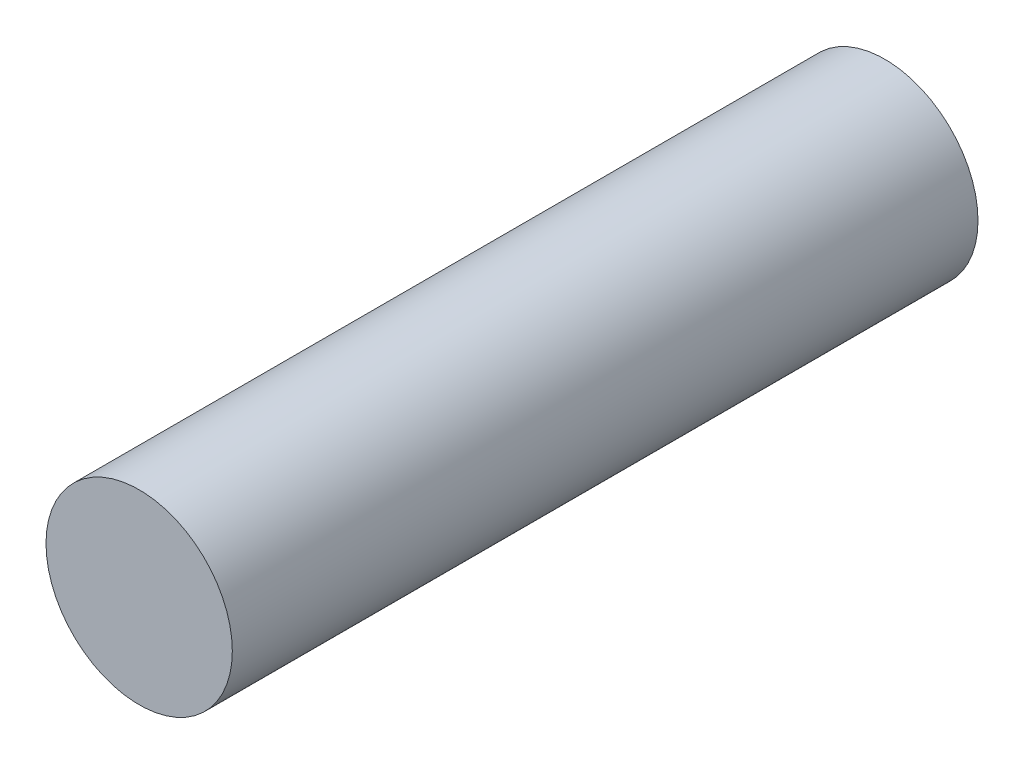
SolidWorks part; units mm, degrees
ref_plane "Front Plane" through (0, 0, 0) normal (0, 0, 1) x (1, 0, 0)
ref_plane "Top Plane" through (0, 0, 0) normal (0, 1, 0) x (1, 0, 0)
ref_plane "Right Plane" through (0, 0, 0) normal (1, 0, 0) x (0, 0, -1)
sketch "Sketch1" plane through (0, 0, 0) normal (0, 0, 1) x (1, 0, 0)
  circle A0 centre (0, 0) radius 4.76
  dimension "D1" = 9.52
extrude "Boss-Extrude1" add sketch "Sketch1" along normal blind 38.1
